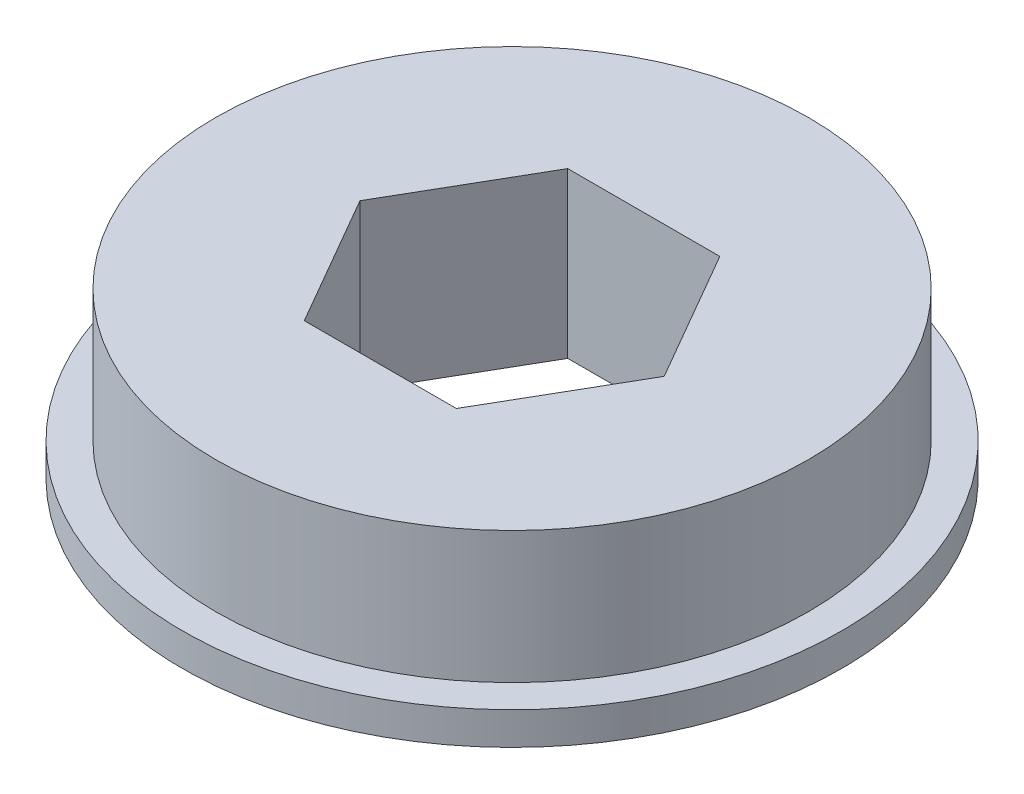
SolidWorks part; units mm, degrees
material "Plain Carbon Steel"
ref_plane "Front Plane" through (0, 0, 0) normal (0, 0, 1) x (1, 0, 0)
ref_plane "Top Plane" through (0, 0, 0) normal (0, 1, 0) x (1, 0, 0)
ref_plane "Right Plane" through (0, 0, 0) normal (1, 0, 0) x (0, 0, -1)
sketch "Sketch1" plane through (0, 0, 0) normal (0, 1, 0) x (1, 0, 0)
  line L1 (7.3323, 0) -> (3.6662, 6.35)
  line L2 (3.6662, 6.35) -> (-3.6662, 6.35)
  line L3 (-3.6662, 6.35) -> (-7.3323, 0)
  line L4 (-7.3323, 0) -> (-3.6662, -6.35)
  line L5 (-3.6662, -6.35) -> (3.6662, -6.35)
  line L6 (3.6662, -6.35) -> (7.3323, 0)
  circle A0 centre (0, 0) radius 14.2875
  circle A1 centre (0, 0) radius 6.35 construction
extrude "Boss-Extrude1" add sketch "Sketch1" along normal blind 6.35
sketch "Sketch2" plane through (0, 0, 0) normal (0, -1, 0) x (1, 0, 0)
  line L1 (-7.3323, 0) -> (-3.6662, -6.35)
  line L2 (-3.6662, -6.35) -> (3.6662, -6.35)
  line L3 (3.6662, -6.35) -> (7.3323, 0)
  line L4 (7.3323, 0) -> (3.6662, 6.35)
  line L5 (3.6662, 6.35) -> (-3.6662, 6.35)
  line L6 (-3.6662, 6.35) -> (-7.3323, 0)
  circle A0 centre (0, 0) radius 15.8877
  circle A1 centre (0, 0) radius 14.2875 construction
  circle A2 centre (0, 0) radius 6.35 construction
  dimension "D1" = 1.6002
extrude "Boss-Extrude2" add sketch "Sketch2" along normal blind 1.5748
